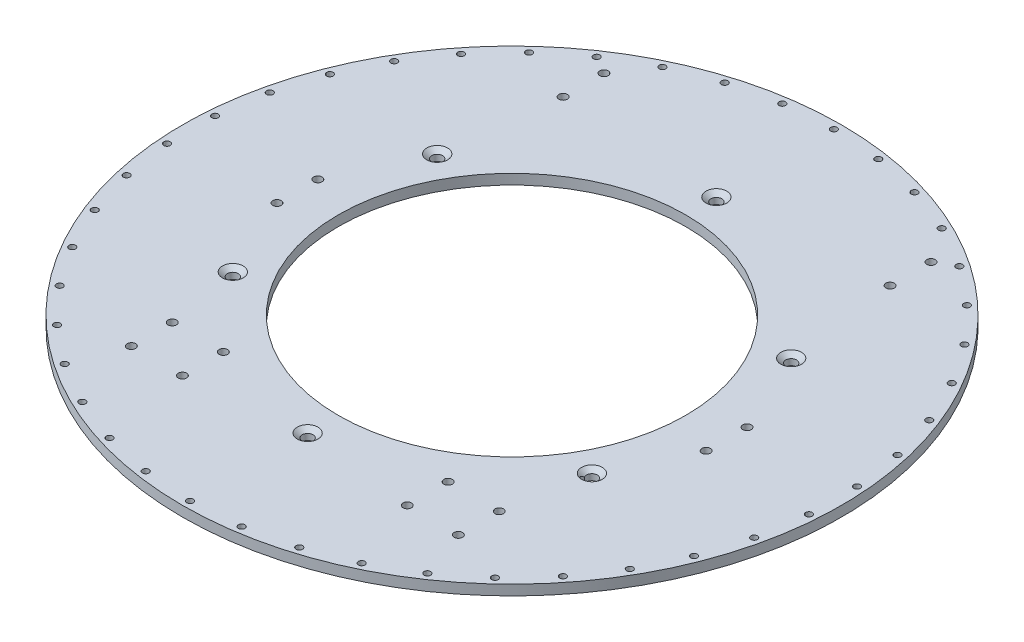
SolidWorks part; units mm, degrees
material "PC High Viscosity"
ref_plane "Front Plane" through (0, 0, 0) normal (0, 0, 1) x (1, 0, 0)
ref_plane "Top Plane" through (0, 0, 0) normal (0, 1, 0) x (1, 0, 0)
ref_plane "Right Plane" through (0, 0, 0) normal (1, 0, 0) x (0, 0, -1)
sketch "Sketch1" plane through (0, 0, 0) normal (0, 1, 0) x (1, 0, 0)
  line L0 (0, 0) -> (0, -95.25) construction
  line L1 (0, -95.25) -> (82.55, -95.25) construction
  line L2 (82.55, -95.25) -> (82.55, -146.0008) construction
  line L3 (82.55, -95.25) -> (88.9, -95.25) construction
  line L4 (88.9, -95.25) -> (88.9, -146.0008) construction
  line L5 (69.85, -109.5375) -> (69.85, -134.9375) construction
  line L6 (101.6, -109.5375) -> (101.6, -134.9375) construction
  line L7 (69.85, -109.5375) -> (101.6, -109.5375) construction
  line L9 (0, 0) -> (0, 133.35) construction
  line L10 (0, 133.35) -> (101.6, 133.35) construction
  line L11 (101.6, 133.35) -> (101.6, 158.75) construction
  line L13 (0, 0) -> (133.35, 0) construction
  line L14 (133.35, 0) -> (133.35, -12.7) construction
  line L15 (133.35, 0) -> (133.35, 12.7) construction
  line L16 (101.6, -134.9375) -> (118.4058, -157.2577) construction
  line L17 (101.6, -134.9375) -> (0, 0) construction
  circle A0 centre (0, 0) radius 107.95
  circle A1 centre (69.85, -109.5375) radius 2.6289
  circle A2 centre (69.85, -134.9375) radius 2.6289
  circle A3 centre (101.6, -109.5375) radius 2.6289
  circle A4 centre (101.6, -134.9375) radius 2.6289
  circle A6 centre (101.6, 133.35) radius 2.6289
  circle A7 centre (101.6, 158.75) radius 2.6289
  circle A11 centre (133.35, -12.7) radius 2.6289
  circle A12 centre (133.35, 12.7) radius 2.6289
  circle A13 centre (0, 0) radius 196.85
  circle A14 centre (-69.85, -134.9375) radius 2.6289
  circle A15 centre (-101.6, -134.9375) radius 2.6289
  circle A16 centre (-101.6, -109.5375) radius 2.6289
  circle A18 centre (-69.85, -109.5375) radius 2.6289
  circle A19 centre (-133.35, -12.7) radius 2.6289
  circle A20 centre (-133.35, 12.7) radius 2.6289
  circle A22 centre (-101.6, 158.75) radius 2.6289
  circle A23 centre (-101.6, 133.35) radius 2.6289
  circle A24 centre (0, 127) radius 3.175
  circle A25 centre (109.9852, 63.5) radius 3.175
  circle A26 centre (109.9852, -63.5) radius 3.175
  circle A27 centre (0, -127) radius 3.175
  circle A28 centre (-109.9852, -63.5) radius 3.175
  circle A29 centre (-109.9852, 63.5) radius 3.175
  point P58 (0, 0)
  dimension "D1" = 82.55
  dimension "D4" = 12.7
  dimension "D5" = 5.2578
  dimension "D7" = 5.2578
  dimension "D8" = 25.4
  dimension "D9" = 5.2578
  dimension "D10" = 5.2578
  dimension "D15" = 6
  dimension "D18" = 5.2578
  dimension "D20" = 5.2578
  dimension "D25" = 5.2578
  dimension "D26" = 5.2578
  dimension "D28" = 393.7
  dimension "D29" = 215.9
  dimension "D19" = 25.4
  dimension "D13" = 127
  dimension "D14" = 6.35
  dimension "D2" = 95.25
  dimension "D3" = 6.35
  dimension "D6" = 25.4
  dimension "D11" = 14.2875
  dimension "D12" = 12.7
  dimension "D16" = 101.6
  dimension "D17" = 228.6
  dimension "D23" = 12.7
  dimension "D24" = 12.7
  dimension "D27" = 133.35
extrude "Boss-Extrude1" add sketch "Sketch1" along normal blind 6.35
ref_plane "Plane1" through (0, 0, 0) normal (1, 0, 0) x (0, 0, -1)
sketch "Sketch3" plane through (0, 6.35, 0) normal (0, 1, 0) x (1, 0, 0)
  circle A0 centre (0, 0) radius 204.7875
  circle A1 centre (0, 0) radius 196.85 construction
  circle A2 centre (0, 0) radius 196.85
  dimension "D1" = 409.575
extrude "Boss-Extrude2" add sketch "Sketch3" against normal up to surface (6.35 mm away) up to face at (0, 0, 196.85)
hole_wizard "CSK for 1/4 Flat Head Machine Screw (100)1" positions "Sketch7" profile "Sketch8" countersink size "1/4" standard "ANSI Inch"
sketch "Sketch7" plane through (0, 6.35, 0) normal (0, 1, 0) x (1, 0, 0)
  circle A0 centre (109.9852, -63.5) radius 3.175 construction
  point P0 (0, 127)
  point P3 (-109.9852, 63.5)
  point P6 (-109.9852, -63.5)
  point P9 (0, -127)
  point P12 (109.9852, -60.325)
  point P16 (109.9852, 63.5)
sketch "Sketch8" plane through (0, 6.35, -127) normal (1, 0, 0) x (0, 0, 1)
  line L0 (0, 0) -> (0, 27.4298)
  line L1 (0, 27.4298) -> (3.3782, 25.4)
  line L2 (3.3782, 25.4) -> (3.3782, 2.5682)
  line L3 (3.3782, 2.5682) -> (6.4389, 0)
  line L5 (6.4389, 0) -> (0, 0)
  line L6 (-3.3782, 2.5682) -> (-6.4389, 0) construction
  line L10 (0, 27.4298) -> (-3.3782, 25.4) construction
  line L11 (0, -6.35) -> (0, 107.95) construction
  dimension "Hole Dia." = 6.7564
  dimension "Hole Depth" = 25.4
  dimension "Near C'Sink Dia." = 12.8778
  dimension "Near C'Sink Angle" = 100
  dimension "Drill Angle" = 118
sketch "Sketch9" plane through (0, 6.35, 0) normal (0, 1, 0) x (1, 0, 0)
  line L0 (-88.9, 171.45) -> (-114.3, 158.75) construction
  line L1 (-114.3, 120.65) -> (-88.9, 120.65) construction
  line L2 (-114.3, 120.65) -> (-114.3, 171.45) construction
  line L3 (-114.3, 171.45) -> (-88.9, 171.45) construction
  line L4 (-88.9, 120.65) -> (-88.9, 171.45) construction
  line L5 (-114.3, 158.75) -> (-101.6, 158.75) construction
  line L6 (0, 0) -> (-116.9792, 162.471) construction
  line L7 (-116.9792, 162.471) -> (-118.5152, 164.6045) construction
  line L8 (-118.5152, 164.6045) -> (-119.6583, 166.1921) construction
  line L9 (-114.3, 158.75) -> (-115.4431, 160.3376) construction
  circle A0 centre (0, 0) radius 204.7875 construction
  circle A1 centre (-101.6, 158.75) radius 2.6289 construction
  circle A2 centre (-116.9792, 162.471) radius 2.6289 construction
  circle A3 centre (0, 0) radius 200.025 construction
  point P14 (-115.4431, 160.3376)
  dimension "D1" = 12.7
  dimension "D2" = 12.7
  dimension "D5" = 5.2578
  dimension "D7" = 400.05
  dimension "D3" = 50.8
  dimension "D4" = 25.4
  dimension "D6" = 200.2023
sketch "Sketch10" plane through (0, 6.35, 0) normal (0, 1, 0) x (1, 0, 0)
  line L0 (0, 0) -> (0, 200.025) construction
  circle A0 centre (0, 0) radius 200.025 construction
  circle A1 centre (0, 200.025) radius 2.0193
  circle A2 centre (29.8122, 197.7909) radius 2.0193
  circle A3 centre (58.9584, 191.1385) radius 2.0193
  circle A4 centre (86.7876, 180.2163) radius 2.0193
  circle A5 centre (112.6781, 165.2684) radius 2.0193
  circle A6 centre (136.0516, 146.6287) radius 2.0193
  circle A7 centre (156.3858, 124.7135) radius 2.0193
  circle A8 centre (173.2267, 100.0125) radius 2.0193
  circle A9 centre (186.198, 73.0773) radius 2.0193
  circle A10 centre (195.01, 44.5097) radius 2.0193
  circle A11 centre (199.4657, 14.9479) radius 2.0193
  circle A12 centre (199.4657, -14.9479) radius 2.0193
  circle A13 centre (195.01, -44.5097) radius 2.0193
  circle A14 centre (186.198, -73.0773) radius 2.0193
  circle A15 centre (173.2267, -100.0125) radius 2.0193
  circle A16 centre (156.3858, -124.7135) radius 2.0193
  circle A17 centre (136.0516, -146.6287) radius 2.0193
  circle A18 centre (112.6781, -165.2684) radius 2.0193
  circle A19 centre (86.7876, -180.2163) radius 2.0193
  circle A20 centre (58.9584, -191.1385) radius 2.0193
  circle A21 centre (29.8122, -197.7909) radius 2.0193
  circle A22 centre (0, -200.025) radius 2.0193
  circle A23 centre (-29.8122, -197.7909) radius 2.0193
  circle A24 centre (-58.9584, -191.1385) radius 2.0193
  circle A25 centre (-86.7876, -180.2163) radius 2.0193
  circle A26 centre (-112.6781, -165.2684) radius 2.0193
  circle A27 centre (-136.0516, -146.6287) radius 2.0193
  circle A28 centre (-156.3858, -124.7135) radius 2.0193
  circle A29 centre (-173.2267, -100.0125) radius 2.0193
  circle A30 centre (-186.198, -73.0773) radius 2.0193
  circle A31 centre (-195.01, -44.5097) radius 2.0193
  circle A32 centre (-199.4657, -14.9479) radius 2.0193
  circle A33 centre (-199.4657, 14.9479) radius 2.0193
  circle A34 centre (-195.01, 44.5097) radius 2.0193
  circle A35 centre (-186.198, 73.0773) radius 2.0193
  circle A36 centre (-173.2267, 100.0125) radius 2.0193
  circle A37 centre (-156.3858, 124.7135) radius 2.0193
  circle A38 centre (-136.0516, 146.6287) radius 2.0193
  circle A39 centre (-112.6781, 165.2684) radius 2.0193
  circle A40 centre (-86.7876, 180.2163) radius 2.0193
  circle A41 centre (-58.9584, 191.1385) radius 2.0193
  circle A42 centre (-29.8122, 197.7909) radius 2.0193
  point P79 (0, 0)
  dimension "D1" = 400.05
  dimension "D2" = 4.0386
  dimension "D3" = 42
extrude "Cut-Extrude1" cut sketch "Sketch10" against normal through all
